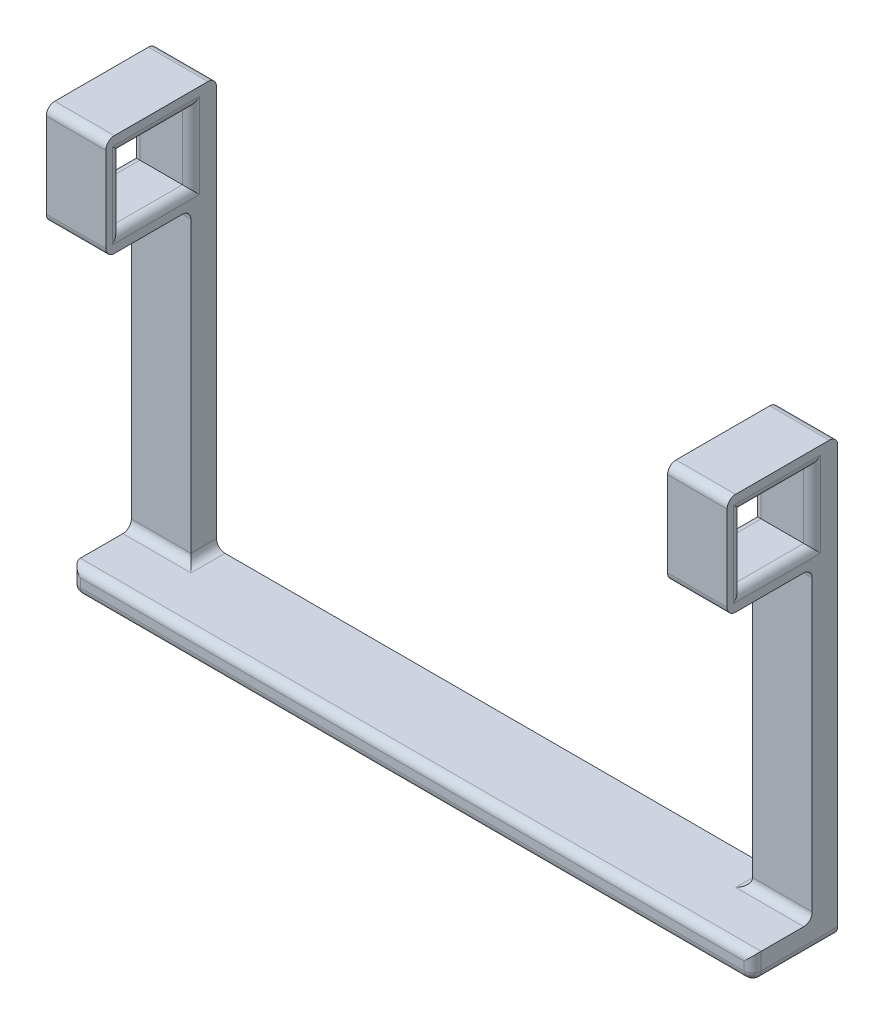
SolidWorks part; units mm, degrees
ref_plane "Front Plane" through (0, 0, 0) normal (0, 0, 1) x (1, 0, 0)
ref_plane "Top Plane" through (0, 0, 0) normal (0, 1, 0) x (1, 0, 0)
ref_plane "Right Plane" through (0, 0, 0) normal (1, 0, 0) x (0, 0, -1)
sketch "Sketch1" plane through (0, 0, 0) normal (0, 0, 1) x (1, 0, 0)
  line L0 (0, 0) -> (40, 0)
  line L1 (40, 0) -> (40, 51)
  line L2 (0, 0) -> (0, 3)
  line L3 (0, 3) -> (33, 3)
  line L4 (33, 3) -> (33, 51)
  line L5 (33, 51) -> (40, 51)
  dimension "D1" = 40
  dimension "D2" = 51
  dimension "D3" = 7
  dimension "D4" = 3
extrude "Boss-Extrude1" add sketch "Sketch1" along normal blind 13
sketch "Sketch2" plane through (40, 0, 0) normal (1, 0, 0) x (0, 0, -1)
  line L0 (-13, 51) -> (-13, 39)
  line L1 (-13, 0) -> (-13, 51) construction
  line L2 (-11.2294, 49) -> (-3, 49)
  line L3 (-3, 49) -> (-3, 41)
  line L4 (-3, 3) -> (-10, 3)
  line L5 (-10, 3) -> (-10, 0)
  line L6 (-13, 0) -> (0, 0) construction
  line L7 (-10, 0) -> (0, 0)
  line L8 (0, 0) -> (0, 51)
  line L9 (0, 51) -> (-13, 51)
  line L15 (-13, 0) -> (-10, 0)
  line L16 (-13, 39) -> (-3, 39)
  line L17 (-11.2294, 49) -> (-11.2294, 41)
  line L18 (-11.2294, 41) -> (-3, 41)
  line L19 (-3, 39) -> (-3, 3)
  line L20 (-13, 39) -> (-13, 0)
  dimension "D1" = 2
  dimension "D2" = 3
  dimension "D3" = 3
  dimension "D4" = 10
  dimension "D5" = 8
  dimension "D6" = 2
  dimension "D7" = 1.7706
extrude "Cut-Extrude1" cut sketch "Sketch2" against normal blind 100
mirror "Mirror2" about plane through (0, 0, 13) normal (1, 0, 0) of bodies 103
fillet "Fillet1" radius 1 30 edges at (36.5, 51, 13) (36.5, 39, 13) (33, 3, 1.5) (0, 3, 10) (33, 41, 7.1147) (33, 49, 7.1147) (33, 45, 11.2294) (40, 0, 5) (36.5, 3, 3) (36.5, 39, 3) (40, 1.5, 10) (0, 0, 10) (40, 49, 7.1147) (40, 45, 11.2294) (40, 41, 7.1147) (-40, 0, 5) (-40, 41, 7.1147) (-40, 45, 11.2294) (36.5, 51, 0) (-33, 49, 7.1147) (-33, 3, 1.5) (-36.5, 3, 3) (-36.5, 39, 13) (-36.5, 51, 13) (-36.5, 51, 0) (-36.5, 39, 3) (-40, 1.5, 10) (-33, 45, 11.2294) (-40, 49, 7.1147) (-33, 41, 7.1147)
